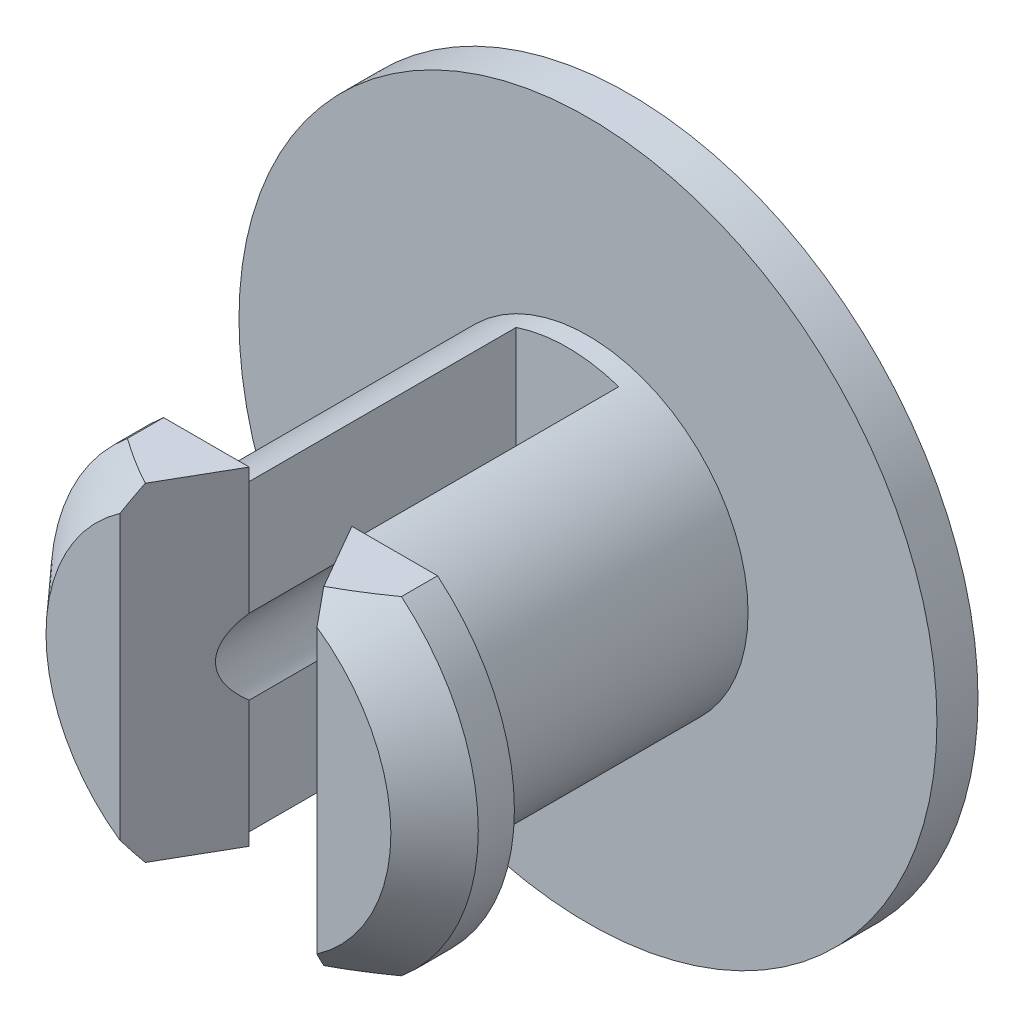
SolidWorks part; units mm, degrees
ref_plane "Front Plane" through (0, 0, 0) normal (0, 0, 1) x (1, 0, 0)
ref_plane "Top Plane" through (0, 0, 0) normal (0, 1, 0) x (1, 0, 0)
ref_plane "Right Plane" through (0, 0, 0) normal (1, 0, 0) x (0, 0, -1)
sketch "Sketch1" plane through (0, 0, 0) normal (0, 0, 1) x (1, 0, 0)
  circle A0 centre (0, 0) radius 8.5
extrude "Boss-Extrude1" add sketch "Sketch1" along normal blind 6 and the other way blind 4.5
sketch "Sketch2" plane through (0, 0, 0) normal (0, 0, 1) x (1, 0, 0)
  circle A0 centre (0, 0) radius 3.9
  circle A1 centre (0, 0) radius 8.5
extrude "Cut-Extrude1" cut sketch "Sketch2" against normal blind 3.5 and the other way blind 3.5
sketch "Sketch3" plane through (0, 0, 3.5) normal (0, 0, -1) x (-1, 0, 0)
  circle A0 centre (0, 0) radius 6
  circle A1 centre (0, 0) radius 8.5
extrude "Cut-Extrude2" cut sketch "Sketch3" against normal blind 3.5
sketch "Sketch5" plane through (0, 0, 0) normal (1, 0, 0) x (0, 0, -1)
  line L0 (-3.5, 5.2087) -> (-4.3792, 5.2087)
  line L2 (-5.5, 6) -> (-5.5, 4.2) construction
  line L4 (-3.5, 6) -> (-5.5, 6) construction
  line L5 (-3.5, 6) -> (-6, 6) construction
  line L6 (-5.5, 4.2) -> (-3.5, 6)
  line L7 (-3.5, 3.9) -> (-3.5, 5.2087)
  line L8 (3.5, 3.9) -> (-3.5, 3.9) construction
  line L9 (-5.5, 4.2) -> (-5.5, 0)
  line L10 (5.775, 0) -> (-5.775, 0) construction
  line L11 (-3.5, 3.9) -> (-3.5, 0)
  line L12 (-3.5, -3.9) -> (-3.5, 3.9) construction
sketch "Sketch6" plane through (0, 0, 0) normal (1, 0, 0) x (0, 0, -1)
  line L2 (-5.5, 0) -> (-5.5, 4.2)
  line L3 (-5.5, 4.2) -> (-4.3792, 5.2087)
  line L4 (-4.3792, 5.2087) -> (-3.5, 5.2087)
  line L5 (-3.5, 5.2087) -> (-3.5, 6)
  line L6 (-3.5, 6) -> (-6, 6)
  line L7 (-6, 6) -> (-6, 0)
  line L8 (-6, 6) -> (-6, -6) construction
  line L9 (-6, 0) -> (-5.5, 0)
  point P1 (-3.5, 5.6)
  point P6 (-6.5688, 0)
sketch "Sketch7" plane through (0, 0, 0) normal (1, 0, 0) x (0, 0, -1)
  line L0 (5.8149, 0) -> (-11.273, 0) construction
  line L1 (6.0879, 0) -> (-6.0879, 0) construction
  point P6 (-2.7291, 0)
revolve "Cut-Revolve1" cut sketch "Sketch6" angle 360 about L0
sketch "Sketch8" plane through (0, 0, 3.5) normal (0, 0, -1) x (-1, 0, 0)
  line L0 (0, 0) -> (0, 4)
  line L1 (0, 5.775) -> (0, -5.775) construction
  line L2 (0, 0) -> (0, -4)
  line L3 (0, -4) -> (-10, -4)
  line L4 (0, -4) -> (10, -4)
  line L5 (0, 4) -> (10, 4)
  line L6 (0, 4) -> (-10, 4)
  line L8 (-10, 4) -> (10, 4)
  line L9 (-10, 4) -> (-10, 8.6474)
  line L10 (-10, 8.6474) -> (10, 8.6474)
  line L11 (10, 4) -> (10, 8.6474)
  line L12 (-10, -4) -> (10, -4)
  line L13 (-10, -4) -> (-10, -8.4188)
  line L14 (-10, -8.4188) -> (10, -8.4188)
  line L15 (10, -4) -> (10, -8.4188)
  point P12 (9.7762, -4.0867)
  circle M4 centre (0, 0) radius 5.2087
  circle M5 centre (0, 0) radius 3.9
extrude "Cut-Extrude4" cut sketch "Sketch8" against normal blind 3.5 contours L6 L5 M5 M4 | L4 L3 M4
sketch "Sketch9" plane through (0, 0, 5.5) normal (0, 0, 1) x (1, 0, 0)
  line L0 (0, 4) -> (-1.25, 4)
  line L3 (-1.2806, 4) -> (1.2806, 4) construction
  line L5 (-1.25, 4) -> (-1.25, -4)
  line L6 (1.2806, -4) -> (-1.2806, -4) construction
  line L7 (-1.25, -4) -> (1.25, -4)
  line L8 (1.25, -4) -> (1.25, 4)
  line L9 (1.25, 4) -> (0, 4)
extrude "Cut-Extrude5" cut sketch "Sketch9" against normal blind 8.5
sketch "Sketch10" plane through (0, 0, -4.5) normal (0, 0, -1) x (-1, 0, 0)
  circle A0 centre (0, 0) radius 1.55
extrude "Cut-Extrude6" cut sketch "Sketch10" against normal up to surface (10 mm away) up to face at (1.9952, 0, 5.5)
sketch "Sketch11" plane through (0, 4, 0) normal (0, 1, 0) x (1, 0, 0)
  line L0 (0, -3.5) -> (-1.25, -3.5)
  line L1 (0, -5.5) -> (0, -3.5) construction
  line L2 (-1.25, -3.5) -> (-1.25, -5.5)
  line L3 (-1.25, -5.5) -> (-2.4, -5.5)
  line L4 (-4.2, -5.5) -> (-1.2806, -5.5) construction
  line L5 (-2.4, -5.5) -> (-1.25, -3.5)
  line L6 (0, -2.7291) -> (0, -6.0017) construction
  line L7 (0, 5.8149) -> (0, -11.273) construction
sketch "Sketch12" plane through (0, 4, 0) normal (0, 1, 0) x (1, 0, 0)
  line L0 (-1.25, -3.5) -> (-1.25, -5.5)
  line L1 (-1.25, -5.5) -> (-2.4, -5.5)
  line L2 (-2.4, -5.5) -> (-1.25, -3.5)
  line L3 (0, -2.7291) -> (0, -6.0017) construction
  line L4 (0, 5.8149) -> (0, -11.273) construction
  line L5 (1.25, -5.5) -> (2.4, -5.5)
  line L6 (1.25, -3.5) -> (1.25, -5.5)
  line L7 (2.4, -5.5) -> (1.25, -3.5)
extrude "Cut-Extrude7" cut sketch "Sketch12" against normal up to surface (8 mm away) contours L2 L0 L1 | L5 L7 L6 up to face at (-2.2396, -4, 4.403)
